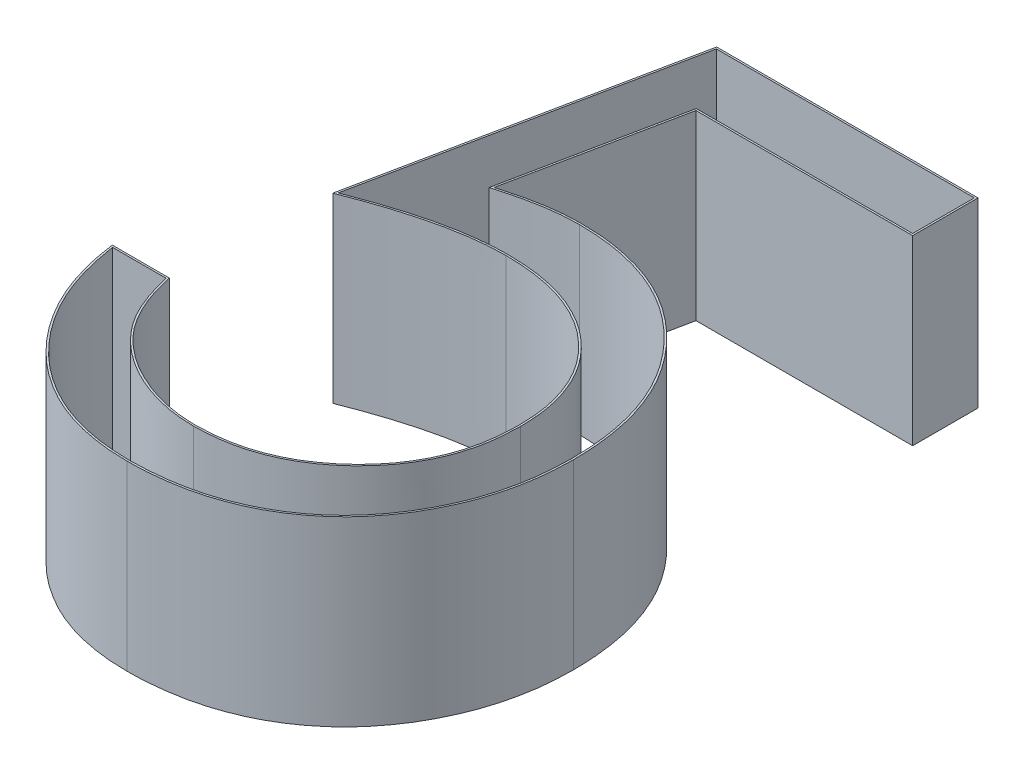
SolidWorks part; units mm, degrees
ref_plane "Front Plane" through (0, 0, 0) normal (0, 0, 1) x (1, 0, 0)
ref_plane "Top Plane" through (0, 0, 0) normal (0, 1, 0) x (1, 0, 0)
ref_plane "Right Plane" through (0, 0, 0) normal (1, 0, 0) x (0, 0, -1)
sketch "Sketch1" plane through (0, 0, 0) normal (0, 1, 0) x (1, 0, 0)
  text T0 "5"
extrude "Boss-Extrude1" add sketch "Sketch1" along normal blind 1
sketch "Sketch2" plane through (0, 1, 0) normal (0, 1, 0) x (1, 0, 0)
  line L18 (2.3233, 3.49) -> (0.9056, 3.49)
  line L19 (0.9056, 3.49) -> (0.5519, 1.7659)
  line L20 (0.4856, 0.8874) -> (0.1912, 0.8874)
  line L21 (0.9412, 2.2065) -> (1.1347, 3.151)
  line L22 (1.1347, 3.151) -> (2.3233, 3.151)
  line L23 (2.3233, 3.151) -> (2.3233, 3.49)
  line L24 (2.3233, 3.49) -> (0.9056, 3.49)
  line L25 (0.9056, 3.49) -> (0.5519, 1.7659)
  line L26 (0.4856, 0.8874) -> (0.1912, 0.8874)
  line L27 (0.9412, 2.2065) -> (1.1347, 3.151)
  line L28 (1.1347, 3.151) -> (2.3233, 3.151)
  line L29 (2.3233, 3.151) -> (2.3233, 3.49)
  spline S24 degree 3 poles (-813.841, 3917.7476) (1.872, -83.4278) (-9.8991, -0.8112) (0.9872, 1.9025) (1.051, 1.9154) (8.7327, 3.0296) (26.1574, -69.1978) (-506.1679, 3969.2902) knots -42.233436 -42.233436 -42.233436 -42.233436 0.5 0.5 0.75 0.75 30.400155 30.400155 30.400155 30.400155 only from (0.5519, 1.7659) to (1.3097, 1.9395)
  spline S25 degree 3 poles (654.3532, 3948.081) (-17.1055, -45.3991) (-3.6907, 2.6161) (1.5242, 1.9222) (1.5767, 1.9112) (1.6801, 1.8799) (1.7307, 1.8577) (1.826, 1.8064) (1.8707, 1.7757) (1.9532, 1.703) (1.9905, 1.6635) (2.055, 1.5764) (2.0821, 1.5278) (2.1245, 1.4272) (2.14, 1.375) (3.0265, -3.4451) (-52.7529, -17.5382) (3894.7005, 920.7606) knots -12.013734 -12.013734 -12.013734 -12.013734 0.125 0.125 0.25 0.25 0.375 0.375 0.5 0.5 0.625 0.625 0.75 0.75 0.875 0.875 11.906477 11.906477 11.906477 11.906477 only from (1.3097, 1.9395) to (2.1638, 1.1568)
  spline S26 degree 3 poles (3951.6467, -631.1944) (-53.298, 20.6444) (3.0587, 6.1146) (2.1388, 0.923) (2.1227, 0.8655) (2.0557, 0.7009) (1.9877, 0.603) (1.8192, 0.4369) (1.7191, 0.3686) (1.5567, 0.3027) (1.5006, 0.2861) (-4.0095, -0.7334) (-19.9555, 59.978) (1032.6544, -3864.3768) knots -10.977165 -10.977165 -10.977165 -10.977165 0.125 0.125 0.25 0.25 0.5 0.5 0.75 0.75 0.875 0.875 12.582858 12.582858 12.582858 12.582858 only from (2.1638, 1.1568) to (1.2655, 0.2592)
  spline S27 degree 3 poles (-711.6254, -3935.5329) (18.8857, 49.1135) (5.3702, -0.4544) (1.0857, 0.2777) (1.0418, 0.2882) (0.9123, 0.3312) (0.8307, 0.3734) (0.6861, 0.483) (0.6233, 0.5513) (-2.5111, 6.1117) (78.4263, 49.8432) (-3423.292, -2067.0973) knots -11.807662 -11.807662 -11.807662 -11.807662 0.125 0.125 0.25 0.25 0.5 0.5 0.75 0.75 17.949363 17.949363 17.949363 17.949363 only from (1.2655, 0.2592) to (0.4856, 0.8874)
  spline S28 degree 3 poles (-3832.9144, -1141.6616) (108.2586, 51.8095) (-3.5803, 8.5045) (0.359, 0.3928) (0.4364, 0.2868) (0.6267, 0.1054) (0.7382, 0.0338) (0.923, -0.0363) (0.9872, -0.0526) (7.2204, -1.1185) (23.6806, 64.0288) (-594.7802, -3955.0866) knots -16.56207 -16.56207 -16.56207 -16.56207 0.25 0.25 0.5 0.5 0.75 0.75 0.875 0.875 12.85235 12.85235 12.85235 12.85235 only from (0.1912, 0.8874) to (1.2473, -0.0797)
  spline S29 degree 3 poles (1628.1005, -3654.1471) (-54.3773, 147.1844) (-8.3168, -3.8247) (1.7943, 0.0306) (1.8657, 0.0667) (2, 0.1545) (2.0632, 0.2068) (2.2296, 0.38) (2.315, 0.5207) (2.402, 0.7451) (2.4232, 0.8239) (3.6225, 7.5141) (-63.0753, 22.6362) (3973.7349, -476.7309) knots -16.366675 -16.366675 -16.366675 -16.366675 0.25 0.25 0.375 0.375 0.5 0.5 0.75 0.75 0.875 0.875 11.306158 11.306158 11.306158 11.306158 only from (1.2473, -0.0797) to (2.4579, 1.1435)
  spline S30 degree 3 poles (3930.9832, 752.8087) (-57.2902, -23.6722) (3.4487, -5.0927) (2.4304, 1.4341) (2.4139, 1.5049) (2.3646, 1.6432) (2.3328, 1.7112) (2.2557, 1.836) (2.2109, 1.8943) (2.1093, 2.0027) (2.0539, 2.051) (1.9338, 2.1352) (1.8681, 2.1712) (1.7313, 2.2263) (1.6606, 2.2461) (-4.529, 3.381) (-23.2978, -60.8286) (1195.7534, 3819.5628) knots -11.113506 -11.113506 -11.113506 -11.113506 0.125 0.125 0.25 0.25 0.375 0.375 0.5 0.5 0.625 0.625 0.75 0.75 0.875 0.875 11.391929 11.391929 11.391929 11.391929 only from (2.4579, 1.1435) to (1.3665, 2.2785)
  spline S31 degree 3 poles (-395.8112, 3982.2031) (12.6722, -30.3339) (5.6227, 2.6682) (1.2607, 2.2733) (1.2255, 2.2701) (1.1905, 2.265) (1.1195, 2.2522) (1.0836, 2.2442) (1.048, 2.2352) (-4.5291, 0.8292) (-4.3434, -22.9385) (-995.7785, 3875.8507) knots -0.013034 -0.013034 -0.013034 -0.013034 0.000106 0.000106 0.000106 0.000212 0.000212 0.000322 0.000322 0.000322 0.017571 0.017571 0.017571 0.017571 only from (1.3665, 2.2785) to (0.9412, 2.2065)
  spline S32 degree 3 poles (0.5519, 1.7659) (0.6737, 1.8127) (0.7973, 1.8552) (0.9872, 1.9025) (1.051, 1.9154) (1.1795, 1.934) (1.2444, 1.9381) (1.3097, 1.9395) knots 0 0 0 0 0.5 0.5 0.75 0.75 1 1 1 1
  spline S33 degree 3 poles (1.3097, 1.9395) (1.3638, 1.9383) (1.4179, 1.9364) (1.5242, 1.9222) (1.5767, 1.9112) (1.6801, 1.8799) (1.7307, 1.8577) (1.826, 1.8064) (1.8707, 1.7757) (1.9532, 1.703) (1.9905, 1.6635) (2.055, 1.5764) (2.0821, 1.5278) (2.1245, 1.4272) (2.14, 1.375) (2.1599, 1.267) (2.1626, 1.2118) (2.1638, 1.1568) knots 0 0 0 0 0.125 0.125 0.25 0.25 0.375 0.375 0.5 0.5 0.625 0.625 0.75 0.75 0.875 0.875 1 1 1 1
  spline S34 degree 3 poles (2.1638, 1.1568) (2.1622, 1.0976) (2.1593, 1.0386) (2.1388, 0.923) (2.1227, 0.8655) (2.0557, 0.7009) (1.9877, 0.603) (1.8192, 0.4369) (1.7191, 0.3686) (1.5567, 0.3027) (1.5006, 0.2861) (1.3842, 0.2646) (1.3248, 0.2609) (1.2655, 0.2592) knots 0 0 0 0 0.125 0.125 0.25 0.25 0.5 0.5 0.75 0.75 0.875 0.875 1 1 1 1
  spline S35 degree 3 poles (1.2655, 0.2592) (1.2199, 0.2605) (1.1745, 0.2625) (1.0857, 0.2777) (1.0418, 0.2882) (0.9123, 0.3312) (0.8307, 0.3734) (0.6861, 0.483) (0.6233, 0.5513) (0.5335, 0.7106) (0.5063, 0.7984) (0.4856, 0.8874) knots 0 0 0 0 0.125 0.125 0.25 0.25 0.5 0.5 0.75 0.75 1 1 1 1
  spline S36 degree 3 poles (0.1912, 0.8874) (0.2114, 0.7571) (0.2435, 0.6305) (0.359, 0.3928) (0.4364, 0.2868) (0.6267, 0.1054) (0.7382, 0.0338) (0.923, -0.0363) (0.9872, -0.0526) (1.116, -0.0746) (1.1815, -0.0784) (1.2473, -0.0797) knots 0 0 0 0 0.25 0.25 0.5 0.5 0.75 0.75 0.875 0.875 1 1 1 1
  spline S37 degree 3 poles (1.2473, -0.0797) (1.4086, -0.0783) (1.5678, -0.0558) (1.7943, 0.0306) (1.8657, 0.0667) (2, 0.1545) (2.0632, 0.2068) (2.2296, 0.38) (2.315, 0.5207) (2.402, 0.7451) (2.4232, 0.8239) (2.4516, 0.9823) (2.4561, 1.0628) (2.4579, 1.1435) knots 0 0 0 0 0.25 0.25 0.375 0.375 0.5 0.5 0.75 0.75 0.875 0.875 1 1 1 1
  spline S38 degree 3 poles (2.4579, 1.1435) (2.4564, 1.2172) (2.4528, 1.2905) (2.4304, 1.4341) (2.4139, 1.5049) (2.3646, 1.6432) (2.3328, 1.7112) (2.2557, 1.836) (2.2109, 1.8943) (2.1093, 2.0027) (2.0539, 2.051) (1.9338, 2.1352) (1.8681, 2.1712) (1.7313, 2.2263) (1.6606, 2.2461) (1.5152, 2.2728) (1.4407, 2.2769) (1.3665, 2.2785) knots 0 0 0 0 0.125 0.125 0.25 0.25 0.375 0.375 0.5 0.5 0.625 0.625 0.75 0.75 0.875 0.875 1 1 1 1
  spline S39 degree 3 poles (1.3665, 2.2785) (1.3312, 2.2775) (1.2959, 2.2765) (1.2255, 2.2701) (1.1905, 2.265) (1.1195, 2.2522) (1.0836, 2.2442) (1.048, 2.2352) (1.0122, 2.2262) (0.9767, 2.2163) (0.9412, 2.2065) knots 0 0 0 0 0.000106 0.000106 0.000212 0.000212 0.000322 0.000322 0.000322 0.000433 0.000433 0.000433 0.000433
  dimension "D1" = 0.01
extrude "Cut-Extrude1" cut sketch "Sketch2" against normal blind 1
